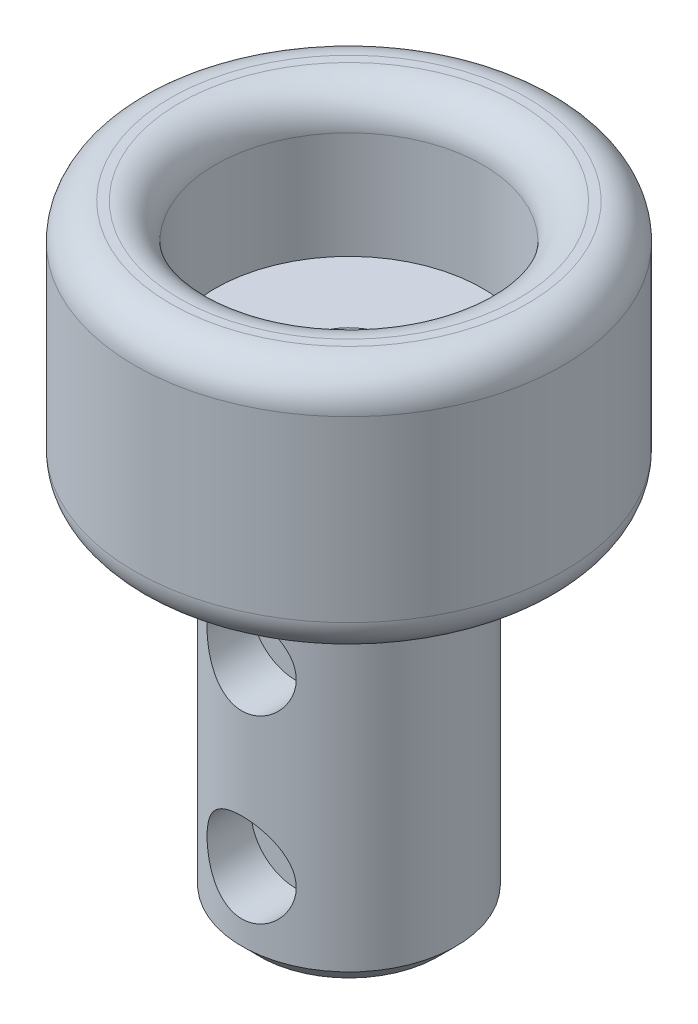
SolidWorks part; units mm, degrees
ref_plane "Vorne" through (0, 0, 0) normal (0, 0, 1) x (1, 0, 0)
ref_plane "Oben" through (0, 0, 0) normal (0, 1, 0) x (1, 0, 0)
ref_plane "Rechts" through (0, 0, 0) normal (1, 0, 0) x (0, 0, -1)
sketch "Skizze1" plane through (0, 0, 0) normal (0, 1, 0) x (1, 0, 0)
  circle A0 centre (0, 0) radius 6
  dimension "D1" = 12
extrude "Aufsatz-Linear austragen1" add sketch "Skizze1" along normal blind 7
sketch "Skizze2" plane through (0, 7, 0) normal (0, 1, 0) x (1, 0, 0)
  circle A0 centre (0, 0) radius 3.75
  dimension "D1" = 7.5
extrude "Schnitt-Linear austragen1" cut sketch "Skizze2" against normal blind 4
sketch "Skizze3" plane through (0, 3, 0) normal (0, 1, 0) x (1, 0, 0)
  circle A0 centre (0, 0) radius 1
  dimension "D1" = 2
extrude "Schnitt-Linear austragen2" cut sketch "Skizze3" against normal blind 4
sketch "Skizze5" plane through (0, 0, 0) normal (0, -1, 0) x (1, 0, 0)
  circle A0 centre (0, 0) radius 1
  circle A1 centre (0, 0) radius 3
  dimension "D1" = 6
  dimension "D2" = 2
extrude "Aufsatz-Linear austragen2" add sketch "Skizze5" along normal blind 10 from offset 0.1 separate body
sketch "Skizze6" plane through (0, 0, 0) normal (0, 0, 1) x (1, 0, 0)
  line L0 (0, -6.6) -> (0, 6.6) construction
  circle A0 centre (0, -2.6354) radius 1.25
  circle A1 centre (0, -7.6847) radius 1.25
  dimension "D1" = 2.5
  dimension "D2" = 2.5
extrude "Schnitt-Linear austragen3" cut sketch "Skizze6" along normal blind 10 from offset 1.5
fillet "Verrundung1" radius 1 3 edges at (0, 7, 3.75) (0, 7, 6) (0, 0, 6)
chamfer "Fase1" distance 0.5 angle 45 2 edges at (0, -0.1, -3) (0, -10.1, -3)
chamfer "Fase2" distance 0.3 angle 45 2 edges at (0, 3, 1) (0, 0, 1)
